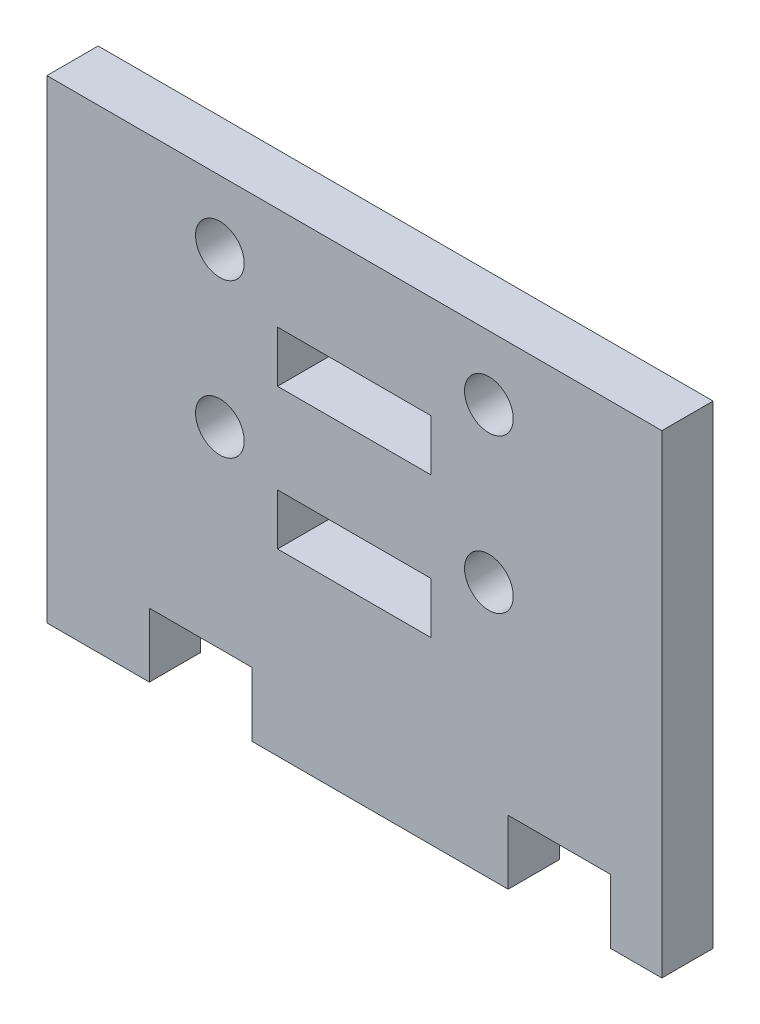
SolidWorks part; units mm, degrees
ref_plane "Front Plane" through (0, 0, 0) normal (0, 0, 1) x (1, 0, 0)
ref_plane "Top Plane" through (0, 0, 0) normal (0, 1, 0) x (1, 0, 0)
ref_plane "Right Plane" through (0, 0, 0) normal (1, 0, 0) x (0, 0, -1)
sketch "Sketch1" plane through (0, 0, 0) normal (0, 0, 1) x (1, 0, 0)
  line L0 (4, 2.5) -> (8, 2.5)
  line L1 (4, 0) -> (0, 0)
  line L2 (0, 18.5) -> (24, 18.5)
  line L3 (0, 0) -> (0, 18.5)
  line L4 (9, 14.5) -> (9, 12.5)
  line L5 (15, 14.5) -> (9, 14.5)
  line L6 (9, 12.5) -> (15, 12.5)
  line L7 (15, 12.5) -> (15, 14.5)
  line L8 (4, 2.5) -> (4, 0)
  line L9 (22, 0) -> (24, 0)
  line L10 (24, 0) -> (24, 18.5)
  line L11 (18, 0) -> (18, 2.5)
  line L12 (15, 7) -> (15, 9)
  line L13 (9, 7) -> (15, 7)
  line L14 (22, 2.5) -> (22, 0)
  line L15 (15, 9) -> (9, 9)
  line L16 (9, 9) -> (9, 7)
  line L17 (18, 2.5) -> (22, 2.5)
  line L18 (8, 0) -> (8, 2.5)
  line L19 (8, 0) -> (18, 0)
  line L20 (12, 12.5) -> (12, 9) construction
  circle A0 centre (6.75, 16) radius 0.95
  circle A1 centre (17.25, 10) radius 0.95
  circle A2 centre (17.25, 16) radius 0.95
  circle A3 centre (6.75, 10) radius 0.95
  dimension "D2" = 4
  dimension "D3" = 18
  dimension "D4" = 2.5
  dimension "D5" = 2
  dimension "D1" = 1.9
  dimension "D6" = 7
  dimension "D7" = 9
  dimension "D8" = 12.5
  dimension "D9" = 15
  dimension "D10" = 6
  dimension "D11" = 10
  dimension "D12" = 18.5
  dimension "D13" = 10.5
extrude "Boss-Extrude1" add sketch "Sketch1" along normal blind 2
equation "\"D13@Sketch1\"= \"fingerWidth@parametersSketch@prostheticParameters.SLDPRT\" - 5.7'Hole distance"
equation "\"D1@Sketch1\"= 1.5 + \"tol1@parametersSketch@prostheticParameters.SLDPRT\""
